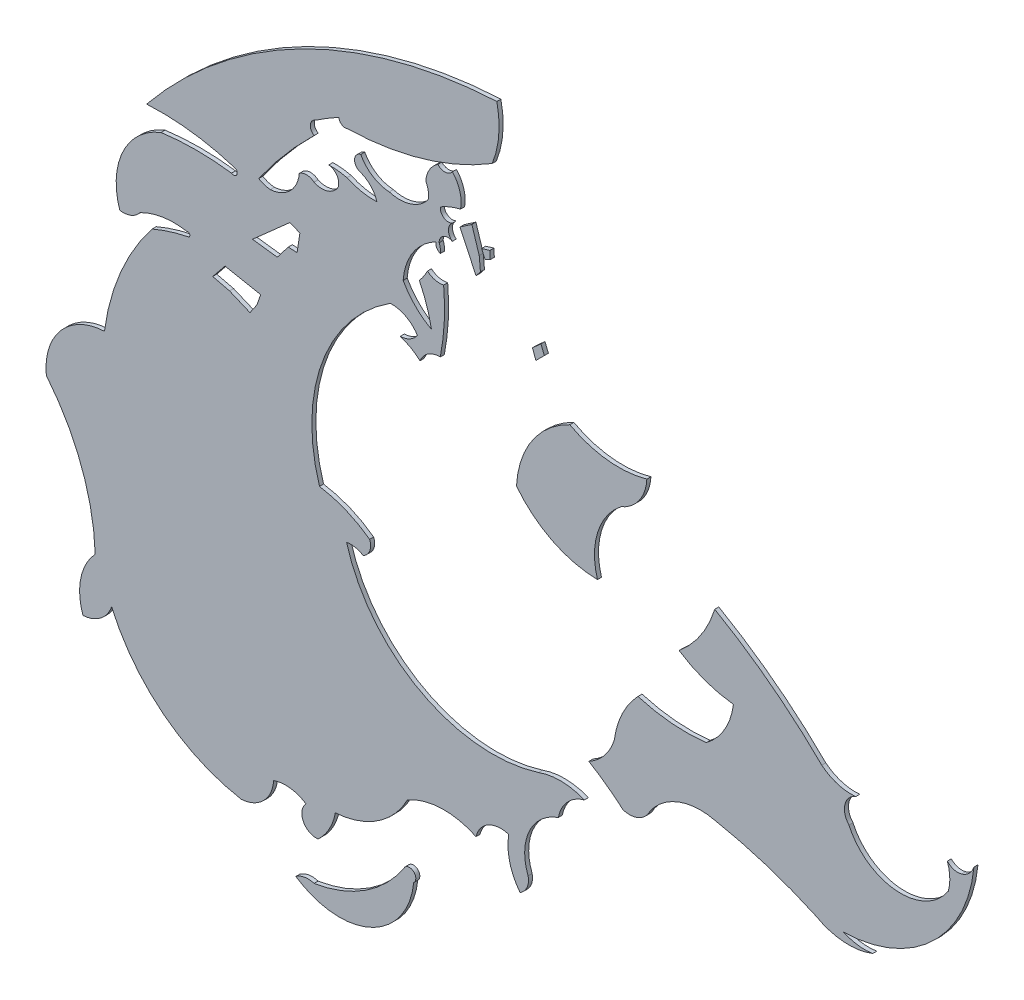
SolidWorks part; units mm, degrees
ref_plane "Alzado" through (0, 0, 0) normal (0, 0, 1) x (1, 0, 0)
ref_plane "Planta" through (0, 0, 0) normal (0, 1, 0) x (1, 0, 0)
ref_plane "Vista lateral" through (0, 0, 0) normal (1, 0, 0) x (0, 0, -1)
sketch "Model" plane through (0, 0, 0) normal (0, 0, 1) x (1, 0, 0)
  line L0 (57.3783, 33.9196) -> (58.3049, 34.7413)
  line L1 (58.3049, 34.7413) -> (58.5496, 34.6364)
  line L2 (58.5496, 34.6364) -> (58.4797, 34.1818)
  line L3 (58.4797, 34.1818) -> (58.2626, 34.1956)
  line L4 (58.2626, 34.1956) -> (57.9894, 33.8415)
  line L5 (57.9894, 33.8415) -> (57.3783, 33.9196)
  line L6 (56.6996, 33.0066) -> (56.3961, 32.6323)
  line L7 (56.3961, 32.6323) -> (56.8109, 32.5311)
  line L8 (56.8109, 32.5311) -> (57.3168, 32.3186)
  line L9 (57.3168, 32.3186) -> (57.4887, 32.5716)
  line L10 (57.4887, 32.5716) -> (57.5798, 32.8346)
  line L11 (57.5798, 32.8346) -> (56.6996, 33.0066)
  line L12 (62.7968, 36.9464) -> (62.5034, 36.744)
  line L13 (62.5034, 36.744) -> (62.9, 35.9)
  line L14 (62.9, 35.9) -> (63.0092, 36.0358)
  line L15 (63.0092, 36.0358) -> (62.9789, 36.3697)
  line L16 (62.9789, 36.3697) -> (62.7968, 36.9464)
  line L17 (63.0396, 36.5518) -> (63.2419, 36.6125)
  line L18 (63.2419, 36.6125) -> (63.2521, 36.4203)
  line L19 (63.2521, 36.4203) -> (63.1205, 36.3596)
  line L20 (63.1205, 36.3596) -> (63.0396, 36.5518)
  line L21 (64.2942, 35.0565) -> (64.504, 35.2453)
  line L22 (64.504, 35.2453) -> (64.5879, 35.0356)
  line L23 (64.5879, 35.0356) -> (64.3781, 34.8258)
  line L24 (64.3781, 34.8258) -> (64.2942, 35.0565)
  arc A1 (63.4139, 39.8856) -> (54.7641, 35.5039) centre (64, 28) ccw
  arc A2 (65.2166, 33.8712) -> (63.9, 31.9) centre (66.2037, 31.7866) ccw
  arc A3 (65.2166, 33.8712) -> (67.1199, 33.6597) centre (66.4275, 36.0988) ccw
  arc A4 (66.4821, 32.75) -> (67.1199, 33.6597) centre (66.0838, 33.7077) ccw
  arc A5 (66.4821, 32.75) -> (65.9, 30.9) centre (67.5418, 31.4) ccw
  arc A6 (63.9, 31.9) -> (65.9, 30.9) centre (65.9428, 33.4857) ccw
  arc A7 (66.9, 28.9) -> (66.3163, 27.6798) centre (68.4861, 27.3915) ccw
  arc A8 (66.9, 28.9) -> (68.5871, 28.7551) centre (68.0941, 32.9102) ccw
  arc A9 (68.5871, 28.7551) -> (69.2584, 29.909) centre (67.5737, 30.117) ccw
  arc A10 (67.9158, 30.3916) -> (69.2584, 29.909) centre (69.5741, 32.8967) ccw
  arc A11 (67.9158, 30.3916) -> (68.7969, 31.7133) centre (66.1629, 32.5147) ccw
  arc A12 (71.4403, 29.6992) -> (68.7969, 31.7133) centre (62.4182, 20.5994) ccw
  arc A13 (71.4403, 29.6992) -> (72.2795, 29.4475) centre (72.1679, 30.5999) ccw
  arc A14 (72.2795, 29.4475) -> (72.1117, 28.7551) centre (72.431, 29.0442) ccw
  arc A15 (72.1117, 28.7551) -> (74.5663, 28.5663) centre (73.391, 29.3378) ccw
  arc A16 (74.5663, 28.5663) -> (74.5418, 29.1981) centre (73.5676, 28.844) ccw
  arc A17 (74.5418, 29.1981) -> (74.9, 29.1) centre (74.8, 29.438) ccw
  arc A18 (74.9, 29.1) -> (75.2, 29.4) centre (74.7601, 29.5399) ccw
  arc A19 (71.9797, 26.3971) -> (75.2, 29.4) centre (71.8978, 29.7131) ccw
  arc A20 (71.9797, 26.3971) -> (72.7, 26.3) centre (72.5, 27.5366) ccw
  arc A21 (71.3, 26.4) -> (72.7, 26.3) centre (72.1056, 27.8278) ccw
  arc A22 (71.3, 26.4) -> (68.8, 27.2) centre (66.73, 16.425) ccw
  arc A23 (68.8, 27.2) -> (67.2, 26.6) centre (68.4432, 25.7182) ccw
  arc A24 (66.5385, 26.2864) -> (67.2, 26.6) centre (66.6872, 26.8271) ccw
  arc A25 (66.5385, 26.2864) -> (65.6886, 26.9056) centre (62.2994, 21.3608) ccw
  arc A26 (65.6886, 26.9056) -> (66.3163, 27.6798) centre (65.0485, 28.0661) ccw
  arc A27 (62.0169, 33.7202) -> (61.5177, 33.3897) centre (62.0033, 33.1985) ccw
  arc A28 (61.5177, 33.3897) -> (61.0292, 33.6677) centre (60.5928, 32.3327) ccw
  arc A29 (61.0292, 33.6677) -> (61.4517, 33.9008) centre (61.0163, 34.1905) ccw
  arc A30 (61.4517, 33.9008) -> (60.7815, 34.2505) centre (60.8146, 33.4969) ccw
  arc A31 (60.7815, 34.2505) -> (59.0333, 29.4599) centre (63.0506, 30.7082) ccw
  arc A32 (60.2719, 28.9463) -> (59.0333, 29.4599) centre (58.6124, 26.6944) ccw
  arc A33 (60.1138, 28.5217) -> (60.2719, 28.9463) centre (59.9607, 28.8204) ccw
  arc A34 (60.1138, 28.5217) -> (59.7, 28.6) centre (59.8, 27.9961) ccw
  arc A35 (59.7, 28.6) -> (64.4431, 26.0441) centre (63.3131, 29.626) ccw
  arc A36 (65.576, 26.0231) -> (64.4431, 26.0441) centre (64.9826, 24.578) ccw
  arc A37 (65.576, 26.0231) -> (64.9332, 25.3267) centre (65.8152, 25.1574) ccw
  arc A38 (64.9332, 25.3267) -> (64.1865, 23.7053) centre (65.3407, 24.1564) ccw
  arc A39 (63.9878, 23.2489) -> (64.1865, 23.7053) centre (63.7665, 23.6167) ccw
  arc A40 (63.708, 24.3503) -> (63.9878, 23.2489) centre (65.1093, 24.1199) ccw
  arc A41 (63.708, 24.3503) -> (62.9, 23.9) centre (63.5091, 23.7572) ccw
  arc A42 (62.9, 23.9) -> (61.208, 23.8433) centre (62.1084, 22.2473) ccw
  arc A43 (59.4247, 22.6719) -> (61.208, 23.8433) centre (59.2777, 24.8389) ccw
  arc A44 (58.9, 20.9) -> (61.1495, 22.3798) centre (58.3881, 24.1278) ccw
  arc A45 (61.3604, 22.1467) -> (61.1495, 22.3798) centre (61.255, 22.2632) ccw
  arc A46 (59.2661, 20.5076) -> (61.3604, 22.1467) centre (59.5281, 22.3305) ccw
  arc A47 (58.4466, 20.8213) -> (59.2661, 20.5076) centre (59.5756, 22.5438) ccw
  arc A48 (58.9, 20.9) -> (58.4466, 20.8213) centre (58.75, 20.419) ccw
  arc A49 (59, 21.9) -> (59.4247, 22.6719) centre (58.0476, 22.9268) ccw
  arc A50 (58.7, 22.5) -> (59, 21.9) centre (58.95, 22.25) ccw
  arc A51 (58.7, 22.5) -> (57.9, 22.6) centre (58.2, 21.75) ccw
  arc A52 (57.1, 21.8) -> (57.9, 22.6) centre (57.05, 22.65) ccw
  arc A53 (53.8984, 24.3166) -> (57.1, 21.8) centre (57.8486, 26.0473) ccw
  arc A54 (53.1915, 23.7778) -> (53.8984, 24.3166) centre (53.1419, 24.576) ccw
  arc A55 (53.4936, 25.238) -> (53.1915, 23.7778) centre (54.5323, 24.2617) ccw
  arc A56 (53.4936, 25.238) -> (52.2852, 28.4604) centre (48.1328, 25.0655) ccw
  arc A57 (53.7202, 30.122) -> (52.2852, 28.4604) centre (53.7859, 28.6148) ccw
  arc A58 (54.9, 32.9) -> (53.7202, 30.122) centre (59.3492, 29.3709) ccw
  arc A59 (55.7963, 33.1786) -> (54.9, 32.9) centre (56.6709, 28.7836) ccw
  arc A60 (55.7963, 33.1786) -> (55.7599, 33.2773) centre (55.7781, 33.228) ccw
  arc A61 (55.7599, 33.2773) -> (54.6, 33.1) centre (55.4408, 31.4821) ccw
  arc A62 (54.1, 32.9) -> (54.6, 33.1) centre (54.1833, 33.4167) ccw
  arc A63 (55.12, 35.0745) -> (54.1, 32.9) centre (55.7536, 33.4508) ccw
  arc A64 (56.8582, 35.0745) -> (55.12, 35.0745) centre (55.9891, 28.6815) ccw
  arc A65 (56.8582, 35.0745) -> (56.9631, 35.2216) centre (56.9106, 35.148) ccw
  arc A66 (56.9631, 35.2216) -> (54.7641, 35.5039) centre (55.1, 29.4141) ccw
  arc A67 (58.9, 36.9) -> (57.5321, 35.2951) centre (66.7092, 28.8589) ccw
  arc A68 (58.9371, 37.2455) -> (58.9, 36.9) centre (58.9957, 37.0645) ccw
  arc A69 (59.514, 37.5951) -> (58.9371, 37.2455) centre (63.1811, 30.8937) ccw
  arc A70 (59.514, 37.5951) -> (59.7293, 37.458) centre (59.6686, 37.6003) ccw
  arc A71 (59.7293, 37.458) -> (63.3, 38.5) centre (59.5779, 44.6159) ccw
  arc A72 (63.3, 38.5) -> (63.4139, 39.8856) centre (61.1406, 39.375) ccw
  arc A73 (61.9567, 37.8096) -> (61.6595, 37.3025) centre (62.3119, 37.2607) ccw
  arc A74 (61.718, 36.934) -> (61.6595, 37.3025) centre (61.1581, 37.034) ccw
  arc A75 (61.9567, 37.8096) -> (62.318, 37.834) centre (62.1277, 37.9647) ccw
  arc A76 (62.518, 37.134) -> (62.318, 37.834) centre (61.718, 37.284) ccw
  arc A77 (62.518, 37.134) -> (62.018, 36.934) centre (62.968, 35.284) ccw
  arc A78 (62.018, 36.934) -> (62.318, 36.734) centre (62.218, 36.909) ccw
  arc A79 (62.318, 36.734) -> (62.3126, 36.3421) centre (62.4639, 36.536) ccw
  arc A80 (62.3126, 36.3421) -> (61.9889, 36.1499) centre (62.2048, 36.155) ccw
  arc A81 (62.018, 35.934) -> (61.9889, 36.1499) centre (61.574, 35.984) ccw
  arc A82 (61.918, 36.134) -> (62.018, 35.934) centre (62.068, 36.084) ccw
  arc A83 (62.0169, 33.7202) -> (62.1, 35.3) centre (56.5437, 34.8) ccw
  arc A84 (61.7, 35.4) -> (62.1, 35.3) centre (62, 35.75) ccw
  arc A85 (61.5, 35.1) -> (61.7, 35.4) centre (60.3732, 36.0679) ccw
  arc A86 (61.8, 34.2) -> (61.5, 35.1) centre (58.35, 33.55) ccw
  arc A87 (61.1, 34.9) -> (61.8, 34.2) centre (62.65, 35.75) ccw
  arc A88 (61.918, 36.134) -> (61.1, 34.9) centre (62.6002, 34.7937) ccw
  arc A89 (60.7558, 36.6219) -> (61.718, 36.934) centre (61.0105, 37.476) ccw
  arc A90 (60.0517, 37.0711) -> (60.7558, 36.6219) centre (60.8039, 37.4738) ccw
  arc A91 (60.0517, 37.0711) -> (60.0152, 36.6947) centre (60.0987, 36.8766) ccw
  arc A92 (60.4523, 36.2577) -> (60.0152, 36.6947) centre (59.8271, 36.0695) ccw
  arc A93 (59.7117, 36.4034) -> (60.4523, 36.2577) centre (60.3819, 37.8548) ccw
  arc A94 (59.7117, 36.4034) -> (59.2625, 36.4519) centre (59.3171, 34.8554) ccw
  arc A95 (59.4932, 36.0877) -> (59.2625, 36.4519) centre (59.2338, 36.1786) ccw
  arc A96 (58.9, 35.9) -> (59.4932, 36.0877) centre (59.0936, 36.3192) ccw
  arc A97 (58.9, 35.9) -> (58.5341, 35.9056) centre (58.7135, 35.6744) ccw
  arc A98 (57.8177, 35.2014) -> (58.5341, 35.9056) centre (57.7651, 35.9713) ccw
  arc A99 (57.5321, 35.2951) -> (57.8177, 35.2014) centre (57.871, 35.8459) ccw
extrude "Saliente-Extruir1" add sketch "Model" along normal blind 0.1
